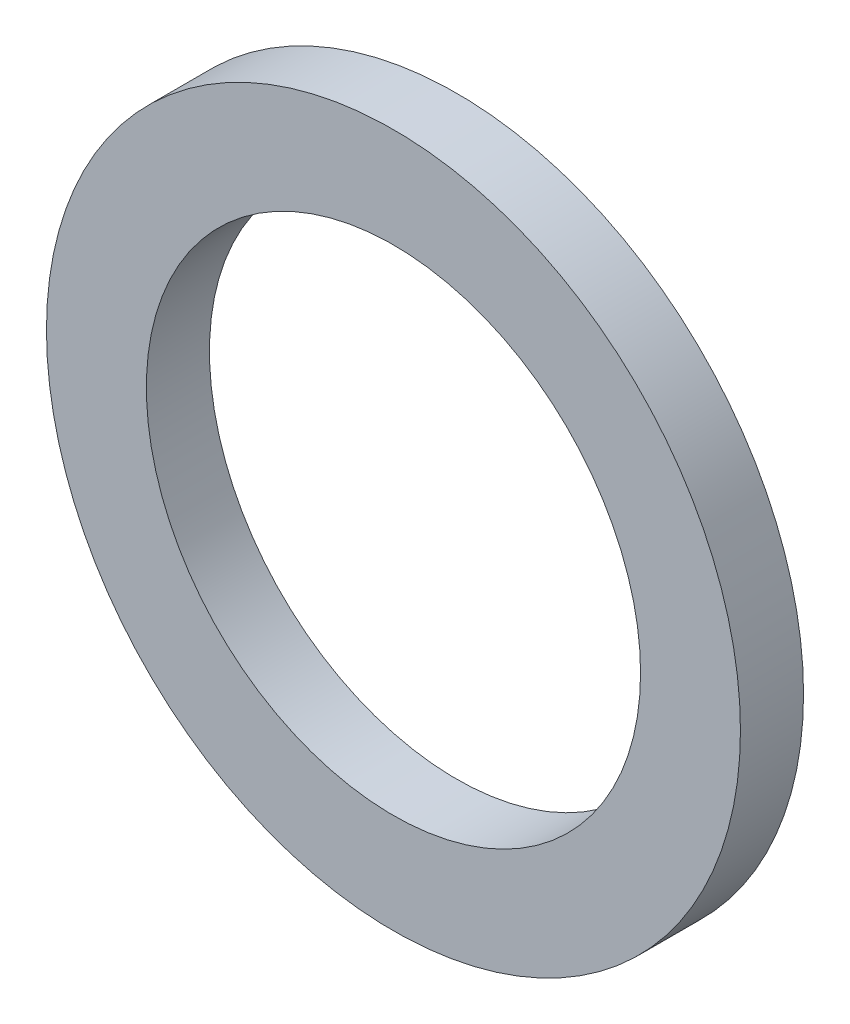
SolidWorks part; units mm, degrees
ref_plane "Plane1" through (0, 0, 0) normal (0, 0, 1) x (1, 0, 0)
ref_plane "Plane2" through (0, 0, 0) normal (0, 1, 0) x (1, 0, 0)
ref_plane "Plane3" through (0, 0, 0) normal (1, 0, 0) x (0, 0, -1)
sketch "Sketch1" plane through (0, 0, 0) normal (0, 0, 1) x (1, 0, 0)
  circle A2 centre (0, 0) radius 8.382
  circle A3 centre (0, 0) radius 5.969
  dimension "D1" = 16.764
  dimension "D2" = 11.938
extrude "Base-Extrude" add sketch "Sketch1" along normal blind 1.524
